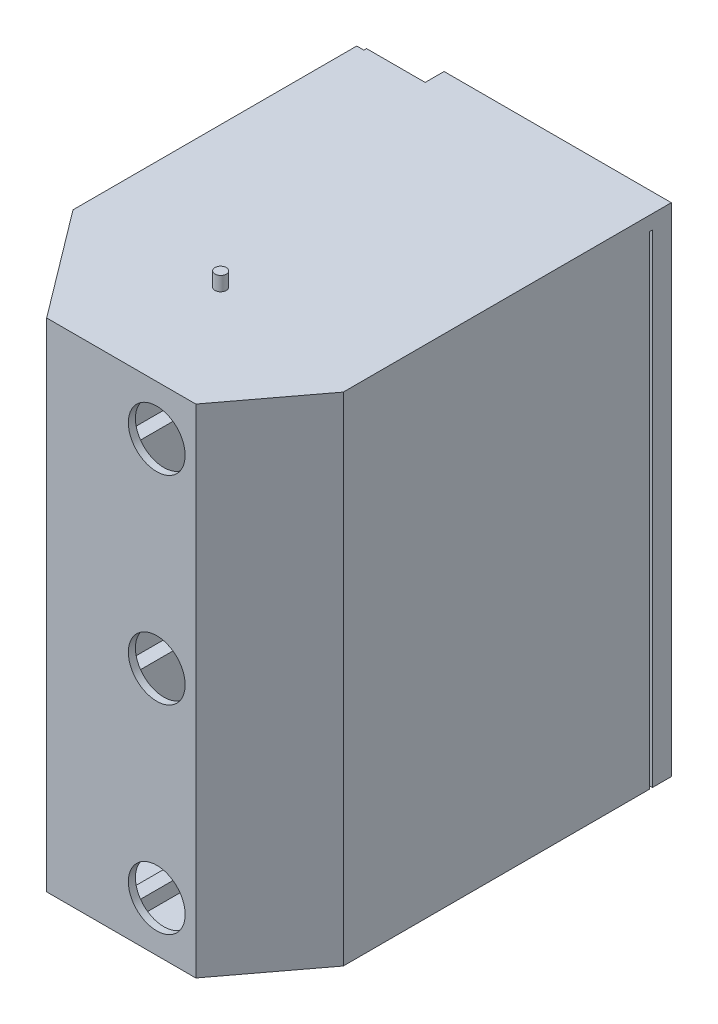
SolidWorks part; units mm, degrees
material "C-Glass Fiber"
ref_plane "Front Plane" through (0, 0, 0) normal (0, 0, 1) x (1, 0, 0)
ref_plane "Top Plane" through (0, 0, 0) normal (0, 1, 0) x (1, 0, 0)
ref_plane "Right Plane" through (0, 0, 0) normal (1, 0, 0) x (0, 0, -1)
sketch "Sketch1" plane through (0, 0, 0) normal (0, 1, 0) x (1, 0, 0)
  line L0 (-50, 0) -> (50, 0)
  line L1 (50, 0) -> (92.1271, 55.9045)
  line L2 (-50, 0) -> (-104.1634, 71.8772)
  line L3 (92.1271, 55.9045) -> (92.1271, 270)
  line L4 (-104.1634, 71.8772) -> (-104.1634, 270)
  point P4 (0, 0)
extrude "Extrude-Thin1" add sketch "Sketch1" along normal blind 350 thin
sketch "Sketch5" plane through (0, 0, 0) normal (0, -1, 0) x (1, 0, 0)
  line L0 (0, 0) -> (0, -250)
extrude "Extrude-Thin3" add sketch "Sketch5" against normal blind 350 thin thin type two direction wall 5 second wall 5
sketch "Sketch8" plane through (5, 0, 0) normal (1, 0, 0) x (0, 0, -1)
  line L0 (0, 350) -> (0, 0) construction
  line L1 (0, 160) -> (150, 160)
  line L2 (0, 160) -> (0, 190)
  line L3 (0, 190) -> (150, 190)
  line L4 (150, 160) -> (150, 190)
extrude "Cut-Extrude2" cut sketch "Sketch8" against normal blind 20
pattern_linear "LPattern4" count 2 spacing 140 along (0, 1, 0) of "Cut-Extrude2"
pattern_linear "LPattern5" count 2 spacing 140 along (0, -1, 0) of "Cut-Extrude2"
sketch "Sketch9" plane through (0, 0, 0) normal (0, -1, 0) x (-1, 0, 0)
  line L0 (104.1634, 270) -> (104.1634, 71.8772)
  line L1 (104.1634, 71.8772) -> (50, 0)
  line L2 (50, 0) -> (-50, 0)
  line L3 (-50, 0) -> (-92.1271, 55.9045)
  line L4 (-92.1271, 55.9045) -> (-92.1271, 270)
  line L5 (-92.1271, 270) -> (104.1634, 270)
extrude "Boss-Extrude1" add sketch "Sketch9" against normal blind 10
sketch "Sketch10" plane through (0, 350, 0) normal (0, 1, 0) x (1, 0, 0)
  line L0 (97.1271, 271.8772) -> (97.1271, 54.2315)
  line L1 (97.1271, 54.2315) -> (50, 0)
  line L2 (50, 0) -> (-50, 0)
  line L3 (-50, 0) -> (-104.1634, 71.8772)
  line L4 (-104.1634, 71.8772) -> (-104.1634, 271.8772)
  line L5 (-104.1634, 271.8772) -> (97.1271, 271.8772)
extrude "Boss-Extrude2" add sketch "Sketch10" against normal blind 10
sketch "Sketch12" plane through (0, 0, 0) normal (0, 0, -1) x (-1, 0, 0)
  circle A0 centre (-25, 35) radius 20
  circle A1 centre (-25, 175) radius 20
  circle A2 centre (-25, 315) radius 20
extrude "Cut-Extrude3" cut sketch "Sketch12" against normal blind 5
sketch "Sketch13" plane through (0, 0, 0) normal (0, 0, -1) x (-1, 0, 0)
  line L0 (-5, 105) -> (-50, 105)
  line L1 (-5, 160) -> (-5, 50) construction
extrude "Extrude-Thin4" add sketch "Sketch13" along normal blind 45 thin
sketch "Sketch15" plane through (0, 110, 0) normal (0, 1, 0) x (1, 0, 0)
  line L0 (50, 0) -> (50, 45)
  line L1 (50, 45) -> (85.7451, 45)
  line L2 (50, 0) -> (85.7451, 45)
extrude "Boss-Extrude4" add sketch "Sketch15" against normal blind 5
pattern_linear "LPattern6" count 2 spacing 140 along (0, 1, 0) of "Extrude-Thin4", "Boss-Extrude4"
sketch "Sketch16" plane through (0, 350, 0) normal (0, 1, 0) x (1, 0, 0)
  circle A0 centre (-10, 75) radius 4
extrude "Boss-Extrude13" add sketch "Sketch16" against normal blind 380 and the other way blind 10 contours A0
scale "Scale2" scale about centroid uniform scaling yes scale factor 0.75
sketch "Sketch17" plane through (0, 0, -27.7603) normal (0, 0, 1) x (1, 0, 0)
  point P0 (17.9269, 280.0443)
  point P1 (17.9269, 175.0443)
  point P3 (17.9269, 70.0443)
sketch "Sketch18" plane through (0, 0, -235.4182) normal (0, 0, -1) x (-1, 0, 0)
  line L0 (-72.0222, 306.2943) -> (78.9456, 306.2943) construction
  line L1 (-72.0222, 43.7943) -> (47.9778, 43.7943)
  line L2 (-72.0222, 43.7943) -> (-72.0222, 306.2943)
  line L3 (-72.0222, 306.2943) -> (47.9778, 306.2943)
  line L4 (47.9778, 43.7943) -> (47.9778, 306.2943)
  dimension "D1" = 120
extrude "Boss-Extrude14" add sketch "Sketch18" along normal blind 10
sketch "Sketch19" plane through (0, 0, -245.4182) normal (0, 0, -1) x (-1, 0, 0)
  text T0 "SEED TANK" font "Century Gothic" height 15
extrude "Cut-Extrude4" cut sketch "Sketch19" against normal blind 1
